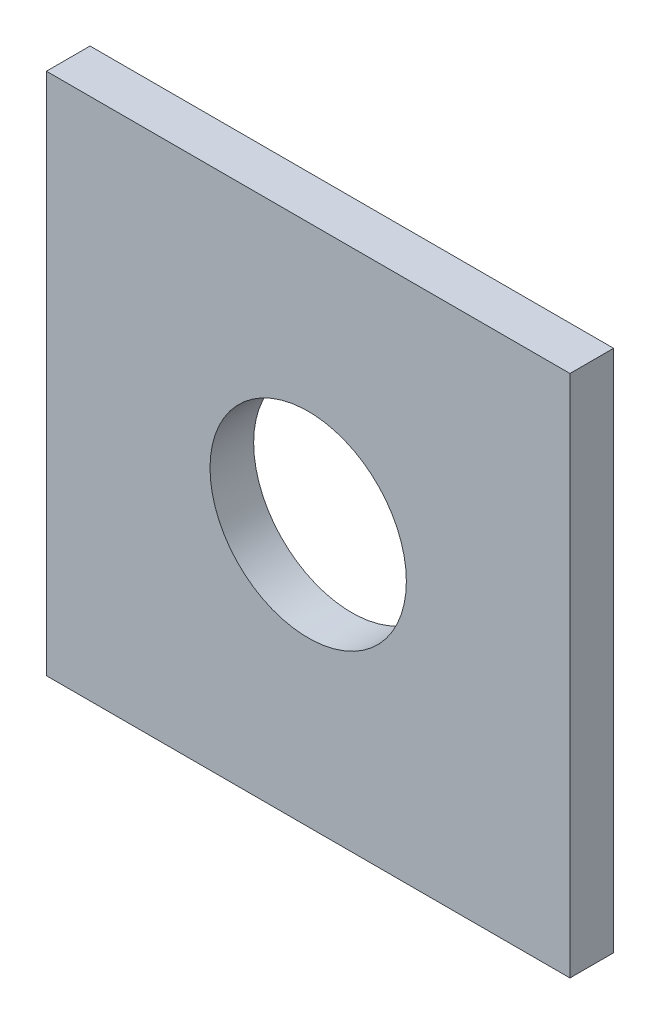
SolidWorks part; units mm, degrees
ref_plane "Front" through (0, 0, 0) normal (0, 0, 1) x (1, 0, 0)
ref_plane "Top" through (0, 0, 0) normal (0, 1, 0) x (1, 0, 0)
ref_plane "Right" through (0, 0, 0) normal (1, 0, 0) x (0, 0, -1)
sketch "Sketch1" plane through (0, 0, 0) normal (0, 0, 1) x (1, 0, 0)
  line L1 (0, 0) -> (-76.2, 0)
  line L2 (0, 0) -> (0, 76.2)
  line L3 (0, 76.2) -> (-76.2, 76.2)
  line L4 (-76.2, 0) -> (-76.2, 76.2)
  dimension "D1" = 76.2
  dimension "D2" = 76.2
extrude "Boss-Extrude1" add sketch "Sketch1" along normal blind 6.35
sketch "Sketch3" plane through (0, 0, 6.35) normal (0, 0, 1) x (1, 0, 0)
  line L0 (-38.1, 76.2) -> (-38.1, 0) construction
  line L1 (0, 76.2) -> (-76.2, 76.2) construction
  line L2 (-76.2, 0) -> (0, 0) construction
  circle A0 centre (-38.1, 38.1) radius 14.2875
  dimension "D1" = 28.575
extrude "Cut-Extrude1" cut sketch "Sketch3" against normal through all
